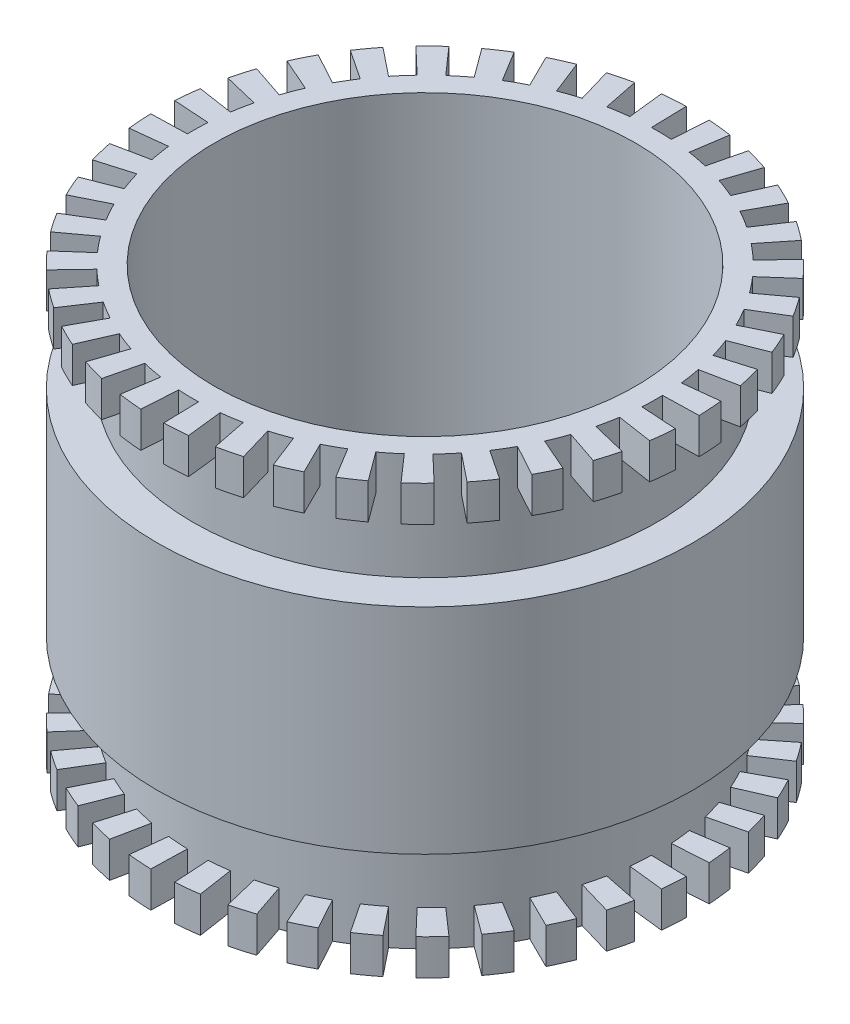
SolidWorks part; units mm, degrees
ref_plane "前视基准面" through (0, 0, 0) normal (0, 0, 1) x (1, 0, 0)
ref_plane "上视基准面" through (0, 0, 0) normal (0, 1, 0) x (1, 0, 0)
ref_plane "右视基准面" through (0, 0, 0) normal (1, 0, 0) x (0, 0, -1)
sketch "Sketch1" plane through (0, 0, 0) normal (0, 1, 0) x (1, 0, 0)
  circle A0 centre (0, 0) radius 26.5 construction
  circle A1 centre (0, 0) radius 29.5
  circle A2 centre (0, 0) radius 37.5
  dimension "D1" = 53
  dimension "D2" = 3
  dimension "D3" = 8
extrude "Boss-Extrude1" add sketch "Sketch1" along normal blind 60
sketch "Sketch2" plane through (0, 0, 0) normal (0, -1, 0) x (1, 0, 0)
  line L0 (-0.7813, 32.4906) -> (-0.9015, 37.4892)
  line L1 (2.0534, 32.4351) -> (2.3693, 37.4251)
  line L2 (4.8725, 32.1327) -> (5.6221, 37.0762)
  line L3 (7.6545, 31.5857) -> (8.8321, 36.4451)
  line L4 (10.3782, 30.7984) -> (11.9749, 35.5366)
  line L5 (13.023, 29.7767) -> (15.0265, 34.3577)
  line L6 (15.5686, 28.5284) -> (17.9638, 32.9173)
  line L7 (17.9958, 27.0629) -> (20.7644, 31.2264)
  line L8 (20.286, 25.3915) -> (23.4069, 29.2979)
  line L9 (22.4218, 23.5268) -> (25.8714, 27.1463)
  line L10 (24.387, 21.4831) -> (28.1389, 24.7882)
  line L11 (26.1666, 19.2759) -> (30.1922, 22.2414)
  line L12 (27.747, 16.922) -> (32.0158, 19.5253)
  line L13 (29.1163, 14.4393) -> (33.5957, 16.6607)
  line L14 (30.264, 11.8467) -> (34.9199, 13.6692)
  line L15 (31.1813, 9.1639) -> (35.9784, 10.5737)
  line L16 (31.8613, 6.4114) -> (36.7631, 7.3978)
  line L17 (32.2989, 3.6101) -> (37.2679, 4.1655)
  line L18 (32.4906, 0.7813) -> (37.4892, 0.9015)
  line L19 (32.4351, -2.0534) -> (37.4251, -2.3693)
  line L20 (32.1327, -4.8725) -> (37.0762, -5.6221)
  line L21 (31.5857, -7.6545) -> (36.4451, -8.8321)
  line L22 (30.7984, -10.3782) -> (35.5366, -11.9749)
  line L23 (29.7767, -13.023) -> (34.3577, -15.0265)
  line L24 (28.5284, -15.5686) -> (32.9173, -17.9638)
  line L25 (27.0629, -17.9958) -> (31.2264, -20.7644)
  line L26 (25.3915, -20.286) -> (29.2979, -23.4069)
  line L27 (23.5268, -22.4218) -> (27.1463, -25.8714)
  line L28 (21.4831, -24.387) -> (24.7882, -28.1389)
  line L29 (19.2759, -26.1666) -> (22.2414, -30.1922)
  line L30 (16.922, -27.747) -> (19.5253, -32.0158)
  line L31 (14.4393, -29.1163) -> (16.6607, -33.5957)
  line L32 (11.8467, -30.264) -> (13.6692, -34.9199)
  line L33 (9.1639, -31.1813) -> (10.5737, -35.9784)
  line L34 (6.4114, -31.8613) -> (7.3978, -36.7631)
  line L35 (3.6101, -32.2989) -> (4.1655, -37.2679)
  line L36 (0.7813, -32.4906) -> (0.9015, -37.4892)
  line L37 (-2.0534, -32.4351) -> (-2.3693, -37.4251)
  line L38 (-4.8725, -32.1327) -> (-5.6221, -37.0762)
  line L39 (-7.6545, -31.5857) -> (-8.8321, -36.4451)
  line L40 (-10.3782, -30.7984) -> (-11.9749, -35.5366)
  line L41 (-13.023, -29.7767) -> (-15.0265, -34.3577)
  line L42 (-15.5686, -28.5284) -> (-17.9638, -32.9173)
  line L43 (-17.9958, -27.0629) -> (-20.7644, -31.2264)
  line L44 (-20.286, -25.3915) -> (-23.4069, -29.2979)
  line L45 (-22.4218, -23.5268) -> (-25.8714, -27.1463)
  line L46 (-24.387, -21.4831) -> (-28.1389, -24.7882)
  line L47 (-26.1666, -19.2759) -> (-30.1922, -22.2414)
  line L48 (-27.747, -16.922) -> (-32.0158, -19.5253)
  line L49 (-29.1163, -14.4393) -> (-33.5957, -16.6607)
  line L50 (-30.264, -11.8467) -> (-34.9199, -13.6692)
  line L51 (-31.1813, -9.1639) -> (-35.9784, -10.5737)
  line L52 (-31.8613, -6.4114) -> (-36.7631, -7.3978)
  line L53 (-32.2989, -3.6101) -> (-37.2679, -4.1655)
  line L54 (-32.4906, -0.7813) -> (-37.4892, -0.9015)
  line L55 (-32.4351, 2.0534) -> (-37.4251, 2.3693)
  line L56 (-32.1327, 4.8725) -> (-37.0762, 5.6221)
  line L57 (-31.5857, 7.6545) -> (-36.4451, 8.8321)
  line L58 (-30.7984, 10.3782) -> (-35.5366, 11.9749)
  line L59 (-29.7767, 13.023) -> (-34.3577, 15.0265)
  line L60 (-28.5284, 15.5686) -> (-32.9173, 17.9638)
  line L61 (-27.0629, 17.9958) -> (-31.2264, 20.7644)
  line L62 (-25.3915, 20.286) -> (-29.2979, 23.4069)
  line L63 (-23.5268, 22.4218) -> (-27.1463, 25.8714)
  line L64 (-21.4831, 24.387) -> (-24.7882, 28.1389)
  line L65 (-19.2759, 26.1666) -> (-22.2414, 30.1922)
  line L66 (-16.922, 27.747) -> (-19.5253, 32.0158)
  line L67 (-14.4393, 29.1163) -> (-16.6607, 33.5957)
  line L68 (-11.8467, 30.264) -> (-13.6692, 34.9199)
  line L69 (-9.1639, 31.1813) -> (-10.5737, 35.9784)
  line L70 (-6.4114, 31.8613) -> (-7.3978, 36.7631)
  line L71 (-3.6101, 32.2989) -> (-4.1655, 37.2679)
  circle A0 centre (0, 0) radius 37.5 construction
  arc A1 (2.3693, 37.4251) -> (-0.9015, 37.4892) centre (0, 0) ccw
  arc A2 (2.0534, 32.4351) -> (-0.7813, 32.4906) centre (0, 0) ccw
  arc A3 (8.8321, 36.4451) -> (5.6221, 37.0762) centre (0, 0) ccw
  arc A4 (7.6545, 31.5857) -> (4.8725, 32.1327) centre (0, 0) ccw
  arc A5 (15.0265, 34.3577) -> (11.9749, 35.5366) centre (0, 0) ccw
  arc A6 (13.023, 29.7767) -> (10.3782, 30.7984) centre (0, 0) ccw
  arc A7 (20.7644, 31.2264) -> (17.9638, 32.9173) centre (0, 0) ccw
  arc A8 (17.9958, 27.0629) -> (15.5686, 28.5284) centre (0, 0) ccw
  arc A9 (25.8714, 27.1463) -> (23.4069, 29.2979) centre (0, 0) ccw
  arc A10 (22.4218, 23.5268) -> (20.286, 25.3915) centre (0, 0) ccw
  arc A11 (30.1922, 22.2414) -> (28.1389, 24.7882) centre (0, 0) ccw
  arc A12 (26.1666, 19.2759) -> (24.387, 21.4831) centre (0, 0) ccw
  arc A13 (33.5957, 16.6607) -> (32.0158, 19.5253) centre (0, 0) ccw
  arc A14 (29.1163, 14.4393) -> (27.747, 16.922) centre (0, 0) ccw
  arc A15 (35.9784, 10.5737) -> (34.9199, 13.6692) centre (0, 0) ccw
  arc A16 (31.1813, 9.1639) -> (30.264, 11.8467) centre (0, 0) ccw
  arc A17 (37.2679, 4.1655) -> (36.7631, 7.3978) centre (0, 0) ccw
  arc A18 (32.2989, 3.6101) -> (31.8613, 6.4114) centre (0, 0) ccw
  arc A19 (37.4251, -2.3693) -> (37.4892, 0.9015) centre (0, 0) ccw
  arc A20 (32.4351, -2.0534) -> (32.4906, 0.7813) centre (0, 0) ccw
  arc A21 (36.4451, -8.8321) -> (37.0762, -5.6221) centre (0, 0) ccw
  arc A22 (31.5857, -7.6545) -> (32.1327, -4.8725) centre (0, 0) ccw
  arc A23 (34.3577, -15.0265) -> (35.5366, -11.9749) centre (0, 0) ccw
  arc A24 (29.7767, -13.023) -> (30.7984, -10.3782) centre (0, 0) ccw
  arc A25 (31.2264, -20.7644) -> (32.9173, -17.9638) centre (0, 0) ccw
  arc A26 (27.0629, -17.9958) -> (28.5284, -15.5686) centre (0, 0) ccw
  arc A27 (27.1463, -25.8714) -> (29.2979, -23.4069) centre (0, 0) ccw
  arc A28 (23.5268, -22.4218) -> (25.3915, -20.286) centre (0, 0) ccw
  arc A29 (22.2414, -30.1922) -> (24.7882, -28.1389) centre (0, 0) ccw
  arc A30 (19.2759, -26.1666) -> (21.4831, -24.387) centre (0, 0) ccw
  arc A31 (16.6607, -33.5957) -> (19.5253, -32.0158) centre (0, 0) ccw
  arc A32 (14.4393, -29.1163) -> (16.922, -27.747) centre (0, 0) ccw
  arc A33 (10.5737, -35.9784) -> (13.6692, -34.9199) centre (0, 0) ccw
  arc A34 (9.1639, -31.1813) -> (11.8467, -30.264) centre (0, 0) ccw
  arc A35 (4.1655, -37.2679) -> (7.3978, -36.7631) centre (0, 0) ccw
  arc A36 (3.6101, -32.2989) -> (6.4114, -31.8613) centre (0, 0) ccw
  arc A37 (-2.3693, -37.4251) -> (0.9015, -37.4892) centre (0, 0) ccw
  arc A38 (-2.0534, -32.4351) -> (0.7813, -32.4906) centre (0, 0) ccw
  arc A39 (-8.8321, -36.4451) -> (-5.6221, -37.0762) centre (0, 0) ccw
  arc A40 (-7.6545, -31.5857) -> (-4.8725, -32.1327) centre (0, 0) ccw
  arc A41 (-15.0265, -34.3577) -> (-11.9749, -35.5366) centre (0, 0) ccw
  arc A42 (-13.023, -29.7767) -> (-10.3782, -30.7984) centre (0, 0) ccw
  arc A43 (-20.7644, -31.2264) -> (-17.9638, -32.9173) centre (0, 0) ccw
  arc A44 (-17.9958, -27.0629) -> (-15.5686, -28.5284) centre (0, 0) ccw
  arc A45 (-25.8714, -27.1463) -> (-23.4069, -29.2979) centre (0, 0) ccw
  arc A46 (-22.4218, -23.5268) -> (-20.286, -25.3915) centre (0, 0) ccw
  arc A47 (-30.1922, -22.2414) -> (-28.1389, -24.7882) centre (0, 0) ccw
  arc A48 (-26.1666, -19.2759) -> (-24.387, -21.4831) centre (0, 0) ccw
  arc A49 (-33.5957, -16.6607) -> (-32.0158, -19.5253) centre (0, 0) ccw
  arc A50 (-29.1163, -14.4393) -> (-27.747, -16.922) centre (0, 0) ccw
  arc A51 (-35.9784, -10.5737) -> (-34.9199, -13.6692) centre (0, 0) ccw
  arc A52 (-31.1813, -9.1639) -> (-30.264, -11.8467) centre (0, 0) ccw
  arc A53 (-37.2679, -4.1655) -> (-36.7631, -7.3978) centre (0, 0) ccw
  arc A54 (-32.2989, -3.6101) -> (-31.8613, -6.4114) centre (0, 0) ccw
  arc A55 (-37.4251, 2.3693) -> (-37.4892, -0.9015) centre (0, 0) ccw
  arc A56 (-32.4351, 2.0534) -> (-32.4906, -0.7813) centre (0, 0) ccw
  arc A57 (-36.4451, 8.8321) -> (-37.0762, 5.6221) centre (0, 0) ccw
  arc A58 (-31.5857, 7.6545) -> (-32.1327, 4.8725) centre (0, 0) ccw
  arc A59 (-34.3577, 15.0265) -> (-35.5366, 11.9749) centre (0, 0) ccw
  arc A60 (-29.7767, 13.023) -> (-30.7984, 10.3782) centre (0, 0) ccw
  arc A61 (-31.2264, 20.7644) -> (-32.9173, 17.9638) centre (0, 0) ccw
  arc A62 (-27.0629, 17.9958) -> (-28.5284, 15.5686) centre (0, 0) ccw
  arc A63 (-27.1463, 25.8714) -> (-29.2979, 23.4069) centre (0, 0) ccw
  arc A64 (-23.5268, 22.4218) -> (-25.3915, 20.286) centre (0, 0) ccw
  arc A65 (-22.2414, 30.1922) -> (-24.7882, 28.1389) centre (0, 0) ccw
  arc A66 (-19.2759, 26.1666) -> (-21.4831, 24.387) centre (0, 0) ccw
  arc A67 (-16.6607, 33.5957) -> (-19.5253, 32.0158) centre (0, 0) ccw
  arc A68 (-14.4393, 29.1163) -> (-16.922, 27.747) centre (0, 0) ccw
  arc A69 (-10.5737, 35.9784) -> (-13.6692, 34.9199) centre (0, 0) ccw
  arc A70 (-9.1639, 31.1813) -> (-11.8467, 30.264) centre (0, 0) ccw
  arc A71 (-4.1655, 37.2679) -> (-7.3978, 36.7631) centre (0, 0) ccw
  arc A72 (-3.6101, 32.2989) -> (-6.4114, 31.8613) centre (0, 0) ccw
  point P150 (0, 0)
  dimension "D2" = 5
  dimension "D1" = 5
  dimension "D3" = 36
extrude "Cut-Extrude1" cut sketch "Sketch2" against normal blind 5
sketch "Sketch3" plane through (0, 5, 0) normal (0, -1, 0) x (1, 0, 0)
  circle A0 centre (0, 0) radius 37.5
  arc A1 (2.3693, 37.4251) -> (-0.9015, 37.4892) centre (0, 0) ccw construction
  circle A2 centre (0, 0) radius 32.5
  arc A3 (7.6545, 31.5857) -> (4.8725, 32.1327) centre (0, 0) ccw construction
extrude "Cut-Extrude2" cut sketch "Sketch3" against normal blind 10
sketch "Sketch4" plane through (0, 60, 0) normal (0, 1, 0) x (1, 0, 0)
  line L0 (-0.7813, 32.4906) -> (-0.9015, 37.4892)
  line L1 (2.0534, 32.4351) -> (2.3693, 37.4251)
  line L2 (4.8725, 32.1327) -> (5.6221, 37.0762)
  line L3 (7.6545, 31.5857) -> (8.8321, 36.4451)
  line L4 (10.3782, 30.7984) -> (11.9749, 35.5366)
  line L5 (13.023, 29.7767) -> (15.0265, 34.3577)
  line L6 (15.5686, 28.5284) -> (17.9638, 32.9173)
  line L7 (17.9958, 27.0629) -> (20.7644, 31.2264)
  line L8 (20.286, 25.3915) -> (23.4069, 29.2979)
  line L9 (22.4218, 23.5268) -> (25.8714, 27.1463)
  line L10 (24.387, 21.4831) -> (28.1389, 24.7882)
  line L11 (26.1666, 19.2759) -> (30.1922, 22.2414)
  line L12 (27.747, 16.922) -> (32.0158, 19.5253)
  line L13 (29.1163, 14.4393) -> (33.5957, 16.6607)
  line L14 (30.264, 11.8467) -> (34.9199, 13.6692)
  line L15 (31.1813, 9.1639) -> (35.9784, 10.5737)
  line L16 (31.8613, 6.4114) -> (36.7631, 7.3978)
  line L17 (32.2989, 3.6101) -> (37.2679, 4.1655)
  line L18 (32.4906, 0.7813) -> (37.4892, 0.9015)
  line L19 (32.4351, -2.0534) -> (37.4251, -2.3693)
  line L20 (32.1327, -4.8725) -> (37.0762, -5.6221)
  line L21 (31.5857, -7.6545) -> (36.4451, -8.8321)
  line L22 (30.7984, -10.3782) -> (35.5366, -11.9749)
  line L23 (29.7767, -13.023) -> (34.3577, -15.0265)
  line L24 (28.5284, -15.5686) -> (32.9173, -17.9638)
  line L25 (27.0629, -17.9958) -> (31.2264, -20.7644)
  line L26 (25.3915, -20.286) -> (29.2979, -23.4069)
  line L27 (23.5268, -22.4218) -> (27.1463, -25.8714)
  line L28 (21.4831, -24.387) -> (24.7882, -28.1389)
  line L29 (19.2759, -26.1666) -> (22.2414, -30.1922)
  line L30 (16.922, -27.747) -> (19.5253, -32.0158)
  line L31 (14.4393, -29.1163) -> (16.6607, -33.5957)
  line L32 (11.8467, -30.264) -> (13.6692, -34.9199)
  line L33 (9.1639, -31.1813) -> (10.5737, -35.9784)
  line L34 (6.4114, -31.8613) -> (7.3978, -36.7631)
  line L35 (3.6101, -32.2989) -> (4.1655, -37.2679)
  line L36 (0.7813, -32.4906) -> (0.9015, -37.4892)
  line L37 (-2.0534, -32.4351) -> (-2.3693, -37.4251)
  line L38 (-4.8725, -32.1327) -> (-5.6221, -37.0762)
  line L39 (-7.6545, -31.5857) -> (-8.8321, -36.4451)
  line L40 (-10.3782, -30.7984) -> (-11.9749, -35.5366)
  line L41 (-13.023, -29.7767) -> (-15.0265, -34.3577)
  line L42 (-15.5686, -28.5284) -> (-17.9638, -32.9173)
  line L43 (-17.9958, -27.0629) -> (-20.7644, -31.2264)
  line L44 (-20.286, -25.3915) -> (-23.4069, -29.2979)
  line L45 (-22.4218, -23.5268) -> (-25.8714, -27.1463)
  line L46 (-24.387, -21.4831) -> (-28.1389, -24.7882)
  line L47 (-26.1666, -19.2759) -> (-30.1922, -22.2414)
  line L48 (-27.747, -16.922) -> (-32.0158, -19.5253)
  line L49 (-29.1163, -14.4393) -> (-33.5957, -16.6607)
  line L50 (-30.264, -11.8467) -> (-34.9199, -13.6692)
  line L51 (-31.1813, -9.1639) -> (-35.9784, -10.5737)
  line L52 (-31.8613, -6.4114) -> (-36.7631, -7.3978)
  line L53 (-32.2989, -3.6101) -> (-37.2679, -4.1655)
  line L54 (-32.4906, -0.7813) -> (-37.4892, -0.9015)
  line L55 (-32.4351, 2.0534) -> (-37.4251, 2.3693)
  line L56 (-32.1327, 4.8725) -> (-37.0762, 5.6221)
  line L57 (-31.5857, 7.6545) -> (-36.4451, 8.8321)
  line L58 (-30.7984, 10.3782) -> (-35.5366, 11.9749)
  line L59 (-29.7767, 13.023) -> (-34.3577, 15.0265)
  line L60 (-28.5284, 15.5686) -> (-32.9173, 17.9638)
  line L61 (-27.0629, 17.9958) -> (-31.2264, 20.7644)
  line L62 (-25.3915, 20.286) -> (-29.2979, 23.4069)
  line L63 (-23.5268, 22.4218) -> (-27.1463, 25.8714)
  line L64 (-21.4831, 24.387) -> (-24.7882, 28.1389)
  line L65 (-19.2759, 26.1666) -> (-22.2414, 30.1922)
  line L66 (-16.922, 27.747) -> (-19.5253, 32.0158)
  line L67 (-14.4393, 29.1163) -> (-16.6607, 33.5957)
  line L68 (-11.8467, 30.264) -> (-13.6692, 34.9199)
  line L69 (-9.1639, 31.1813) -> (-10.5737, 35.9784)
  line L70 (-6.4114, 31.8613) -> (-7.3978, 36.7631)
  line L71 (-3.6101, 32.2989) -> (-4.1655, 37.2679)
  line L72 (-0.7813, 32.4906) -> (0, 0) construction
  line L73 (0, 0) -> (2.0534, 32.4351) construction
  arc A0 (2.3693, 37.4251) -> (-0.9015, 37.4892) centre (0, 0) ccw
  arc A1 (2.0534, 32.4351) -> (-0.7813, 32.4906) centre (0, 0) ccw
  arc A2 (8.8321, 36.4451) -> (5.6221, 37.0762) centre (0, 0) ccw
  arc A3 (7.6545, 31.5857) -> (4.8725, 32.1327) centre (0, 0) ccw
  arc A4 (15.0265, 34.3577) -> (11.9749, 35.5366) centre (0, 0) ccw
  arc A5 (13.023, 29.7767) -> (10.3782, 30.7984) centre (0, 0) ccw
  arc A6 (20.7644, 31.2264) -> (17.9638, 32.9173) centre (0, 0) ccw
  arc A7 (17.9958, 27.0629) -> (15.5686, 28.5284) centre (0, 0) ccw
  arc A8 (25.8714, 27.1463) -> (23.4069, 29.2979) centre (0, 0) ccw
  arc A9 (22.4218, 23.5268) -> (20.286, 25.3915) centre (0, 0) ccw
  arc A10 (30.1922, 22.2414) -> (28.1389, 24.7882) centre (0, 0) ccw
  arc A11 (26.1666, 19.2759) -> (24.387, 21.4831) centre (0, 0) ccw
  arc A12 (33.5957, 16.6607) -> (32.0158, 19.5253) centre (0, 0) ccw
  arc A13 (29.1163, 14.4393) -> (27.747, 16.922) centre (0, 0) ccw
  arc A14 (35.9784, 10.5737) -> (34.9199, 13.6692) centre (0, 0) ccw
  arc A15 (31.1813, 9.1639) -> (30.264, 11.8467) centre (0, 0) ccw
  arc A16 (37.2679, 4.1655) -> (36.7631, 7.3978) centre (0, 0) ccw
  arc A17 (32.2989, 3.6101) -> (31.8613, 6.4114) centre (0, 0) ccw
  arc A18 (37.4251, -2.3693) -> (37.4892, 0.9015) centre (0, 0) ccw
  arc A19 (32.4351, -2.0534) -> (32.4906, 0.7813) centre (0, 0) ccw
  arc A20 (36.4451, -8.8321) -> (37.0762, -5.6221) centre (0, 0) ccw
  arc A21 (31.5857, -7.6545) -> (32.1327, -4.8725) centre (0, 0) ccw
  arc A22 (34.3577, -15.0265) -> (35.5366, -11.9749) centre (0, 0) ccw
  arc A23 (29.7767, -13.023) -> (30.7984, -10.3782) centre (0, 0) ccw
  arc A24 (31.2264, -20.7644) -> (32.9173, -17.9638) centre (0, 0) ccw
  arc A25 (27.0629, -17.9958) -> (28.5284, -15.5686) centre (0, 0) ccw
  arc A26 (27.1463, -25.8714) -> (29.2979, -23.4069) centre (0, 0) ccw
  arc A27 (23.5268, -22.4218) -> (25.3915, -20.286) centre (0, 0) ccw
  arc A28 (22.2414, -30.1922) -> (24.7882, -28.1389) centre (0, 0) ccw
  arc A29 (19.2759, -26.1666) -> (21.4831, -24.387) centre (0, 0) ccw
  arc A30 (16.6607, -33.5957) -> (19.5253, -32.0158) centre (0, 0) ccw
  arc A31 (14.4393, -29.1163) -> (16.922, -27.747) centre (0, 0) ccw
  arc A32 (10.5737, -35.9784) -> (13.6692, -34.9199) centre (0, 0) ccw
  arc A33 (9.1639, -31.1813) -> (11.8467, -30.264) centre (0, 0) ccw
  arc A34 (4.1655, -37.2679) -> (7.3978, -36.7631) centre (0, 0) ccw
  arc A35 (3.6101, -32.2989) -> (6.4114, -31.8613) centre (0, 0) ccw
  arc A36 (-2.3693, -37.4251) -> (0.9015, -37.4892) centre (0, 0) ccw
  arc A37 (-2.0534, -32.4351) -> (0.7813, -32.4906) centre (0, 0) ccw
  arc A38 (-8.8321, -36.4451) -> (-5.6221, -37.0762) centre (0, 0) ccw
  arc A39 (-7.6545, -31.5857) -> (-4.8725, -32.1327) centre (0, 0) ccw
  arc A40 (-15.0265, -34.3577) -> (-11.9749, -35.5366) centre (0, 0) ccw
  arc A41 (-13.023, -29.7767) -> (-10.3782, -30.7984) centre (0, 0) ccw
  arc A42 (-20.7644, -31.2264) -> (-17.9638, -32.9173) centre (0, 0) ccw
  arc A43 (-17.9958, -27.0629) -> (-15.5686, -28.5284) centre (0, 0) ccw
  arc A44 (-25.8714, -27.1463) -> (-23.4069, -29.2979) centre (0, 0) ccw
  arc A45 (-22.4218, -23.5268) -> (-20.286, -25.3915) centre (0, 0) ccw
  arc A46 (-30.1922, -22.2414) -> (-28.1389, -24.7882) centre (0, 0) ccw
  arc A47 (-26.1666, -19.2759) -> (-24.387, -21.4831) centre (0, 0) ccw
  arc A48 (-33.5957, -16.6607) -> (-32.0158, -19.5253) centre (0, 0) ccw
  arc A49 (-29.1163, -14.4393) -> (-27.747, -16.922) centre (0, 0) ccw
  arc A50 (-35.9784, -10.5737) -> (-34.9199, -13.6692) centre (0, 0) ccw
  arc A51 (-31.1813, -9.1639) -> (-30.264, -11.8467) centre (0, 0) ccw
  arc A52 (-37.2679, -4.1655) -> (-36.7631, -7.3978) centre (0, 0) ccw
  arc A53 (-32.2989, -3.6101) -> (-31.8613, -6.4114) centre (0, 0) ccw
  arc A54 (-37.4251, 2.3693) -> (-37.4892, -0.9015) centre (0, 0) ccw
  arc A55 (-32.4351, 2.0534) -> (-32.4906, -0.7813) centre (0, 0) ccw
  arc A56 (-36.4451, 8.8321) -> (-37.0762, 5.6221) centre (0, 0) ccw
  arc A57 (-31.5857, 7.6545) -> (-32.1327, 4.8725) centre (0, 0) ccw
  arc A58 (-34.3577, 15.0265) -> (-35.5366, 11.9749) centre (0, 0) ccw
  arc A59 (-29.7767, 13.023) -> (-30.7984, 10.3782) centre (0, 0) ccw
  arc A60 (-31.2264, 20.7644) -> (-32.9173, 17.9638) centre (0, 0) ccw
  arc A61 (-27.0629, 17.9958) -> (-28.5284, 15.5686) centre (0, 0) ccw
  arc A62 (-27.1463, 25.8714) -> (-29.2979, 23.4069) centre (0, 0) ccw
  arc A63 (-23.5268, 22.4218) -> (-25.3915, 20.286) centre (0, 0) ccw
  arc A64 (-22.2414, 30.1922) -> (-24.7882, 28.1389) centre (0, 0) ccw
  arc A65 (-19.2759, 26.1666) -> (-21.4831, 24.387) centre (0, 0) ccw
  arc A66 (-16.6607, 33.5957) -> (-19.5253, 32.0158) centre (0, 0) ccw
  arc A67 (-14.4393, 29.1163) -> (-16.922, 27.747) centre (0, 0) ccw
  arc A68 (-10.5737, 35.9784) -> (-13.6692, 34.9199) centre (0, 0) ccw
  arc A69 (-9.1639, 31.1813) -> (-11.8467, 30.264) centre (0, 0) ccw
  arc A70 (-4.1655, 37.2679) -> (-7.3978, 36.7631) centre (0, 0) ccw
  arc A71 (-3.6101, 32.2989) -> (-6.4114, 31.8613) centre (0, 0) ccw
  point P145 (0, 0)
  dimension "D2" = 5
  dimension "D1" = 5
extrude "Cut-Extrude3" cut sketch "Sketch4" against normal blind 5
sketch "Sketch5" plane through (0, 55, 0) normal (0, 1, 0) x (1, 0, 0)
  circle A0 centre (0, 0) radius 32.5
  circle A1 centre (0, 0) radius 37.5
  arc A2 (-20.7644, -31.2264) -> (-17.9638, -32.9173) centre (0, 0) ccw construction
  arc A3 (-22.4218, -23.5268) -> (-20.286, -25.3915) centre (0, 0) ccw construction
extrude "Cut-Extrude4" cut sketch "Sketch5" against normal blind 10
